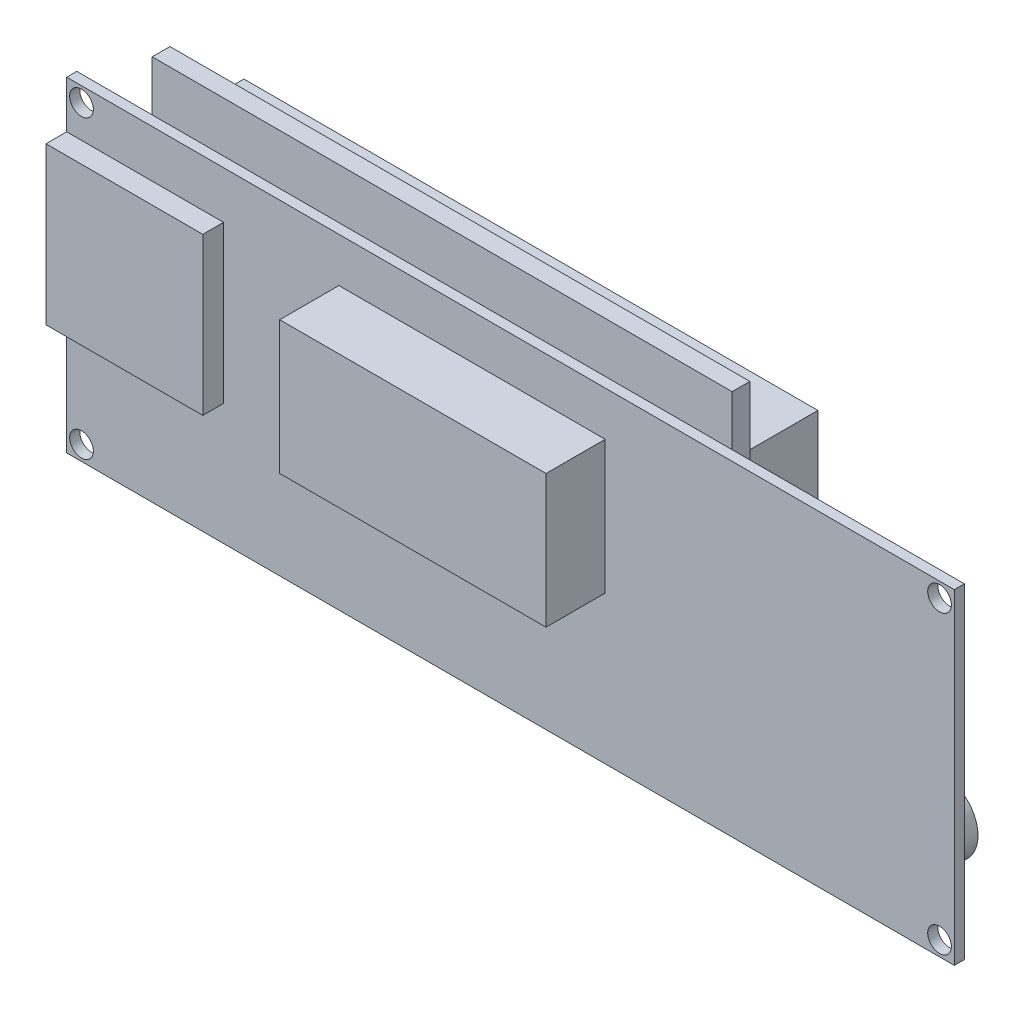
SolidWorks part; units mm, degrees
ref_plane "Front Plane" through (0, 0, 0) normal (0, 0, 1) x (1, 0, 0)
ref_plane "Top Plane" through (0, 0, 0) normal (0, 1, 0) x (1, 0, 0)
ref_plane "Right Plane" through (0, 0, 0) normal (1, 0, 0) x (0, 0, -1)
sketch "Sketch2" plane through (0, 0, 0) normal (0, 0, 1) x (1, 0, 0)
  line L0 (75, 27.5) -> (75, -27.5) construction
  line L1 (35.75, 27.5) -> (75, 27.5) construction
  line L2 (-75, -27.5) -> (75, -27.5) construction
  line L3 (-75, 27.5) -> (-75, -27.5) construction
  line L4 (-75, 27.5) -> (-62.25, 27.5) construction
  line L5 (-62.25, 27.5) -> (35.75, 27.5) construction
  line L6 (75, 27.5) -> (75, -27.5)
  line L7 (35.75, 27.5) -> (75, 27.5)
  line L8 (-75, -27.5) -> (75, -27.5)
  line L9 (-75, 27.5) -> (-75, -27.5)
  line L10 (-75, 27.5) -> (-62.25, 27.5)
  line L11 (-62.25, 27.5) -> (35.75, 27.5)
  circle A0 centre (-72.5, -25) radius 2 construction
  circle A1 centre (-72.5, 25) radius 2 construction
  circle A2 centre (72.5, -25) radius 2 construction
  circle A3 centre (72.5, 25) radius 2 construction
  circle A4 centre (-72.5, -25) radius 2
  circle A5 centre (-72.5, 25) radius 2
  circle A6 centre (72.5, -25) radius 2
  circle A7 centre (72.5, 25) radius 2
extrude "Boss-Extrude1" add sketch "Sketch2" along normal up to vertex (1.7 mm away)
sketch "Sketch3" plane through (0, 0, 0) normal (0, 0, 1) x (1, 0, 0)
  line L1 (-62.25, 36) -> (35.75, 36)
  line L2 (-62.25, 36) -> (-62.25, -24)
  line L3 (-62.25, -24) -> (35.75, -24)
  line L4 (35.75, 36) -> (35.75, -24)
  dimension "D1" = 60
extrude "Boss-Extrude2" add sketch "Sketch3" against normal up to vertex (3 mm away)
sketch "Sketch4" plane through (0, 0, 0) normal (0, 0, 1) x (1, 0, 0)
  line L1 (-61.75, -14.5) -> (35.25, -14.5)
  line L2 (-61.75, -14.5) -> (-61.75, 25.5)
  line L3 (-61.75, 25.5) -> (35.25, 25.5)
  line L4 (35.25, -14.5) -> (35.25, 25.5)
extrude "Boss-Extrude3" add sketch "Sketch4" against normal up to vertex (15 mm away)
sketch "Sketch5" plane through (0, 0, 0) normal (0, 0, 1) x (1, 0, 0)
  line L1 (59, 23) -> (65, 23)
  line L2 (59, 23) -> (59, 17)
  line L3 (59, 17) -> (65, 17)
  line L4 (65, 23) -> (65, 17)
  line L5 (59, 23) -> (65, 17) construction
  line L6 (59, 17) -> (65, 23) construction
  point P0 (62, 20)
  dimension "D1" = 6
  dimension "D2" = 6
extrude "Boss-Extrude4" add sketch "Sketch5" against normal blind 3
sketch "Sketch6" plane through (0, 0, -3) normal (0, 0, -1) x (-1, 0, 0)
  circle A0 centre (-62, 20) radius 1.75
  point P3 (-75, 27.5)
extrude "Boss-Extrude5" add sketch "Sketch6" along normal blind 0.65
sketch "Sketch7" plane through (0, 0, 0) normal (0, 0, 1) x (1, 0, 0)
  line L1 (55.875, -3.375) -> (68.125, -3.375)
  line L2 (55.875, -3.375) -> (55.875, 8.375)
  line L3 (55.875, 8.375) -> (68.125, 8.375)
  line L4 (68.125, -3.375) -> (68.125, 8.375)
  line L5 (55.875, -3.375) -> (68.125, 8.375) construction
  line L6 (55.875, 8.375) -> (68.125, -3.375) construction
  point P0 (62, 2.5)
  dimension "D1" = 11.75
  dimension "D2" = 12.25
extrude "Boss-Extrude6" add sketch "Sketch7" against normal blind 4.5
sketch "Sketch8" plane through (0, 0, 0) normal (0, 0, 1) x (1, 0, 0)
  circle A0 centre (62, -17.5) radius 6
  circle A1 centre (62, -17.5) radius 6 construction
extrude "Boss-Extrude7" add sketch "Sketch8" against normal blind 9.3
sketch "Sketch9" plane through (0, 0, 1.7) normal (0, 0, 1) x (1, 0, 0)
  line L0 (-75, -27.5) -> (75, -27.5) construction
  line L1 (16, -2.5) -> (-29, -2.5)
  line L2 (16, -2.5) -> (16, 20)
  line L3 (16, 20) -> (-29, 20)
  line L4 (-29, -2.5) -> (-29, 20)
  line L5 (-75, 27.5) -> (-75, -27.5) construction
  dimension "D1" = 45
  dimension "D2" = 22.5
  dimension "D3" = 25
  dimension "D4" = 46
extrude "Boss-Extrude8" add sketch "Sketch9" along normal up to vertex (10 mm away)
sketch "Sketch10" plane through (0, 0, 1.7) normal (0, 0, 1) x (1, 0, 0)
  line L0 (-75, 27.5) -> (-75, -27.5) construction
  line L1 (-75, 19.5) -> (-48.5, 19.5)
  line L2 (-75, 19.5) -> (-75, -7)
  line L3 (-75, -7) -> (-48.5, -7)
  line L4 (-48.5, 19.5) -> (-48.5, -7)
  line L5 (75, 27.5) -> (-75, 27.5) construction
  dimension "D1" = 26.5
  dimension "D2" = 26.5
  dimension "D3" = 8
extrude "Boss-Extrude9" add sketch "Sketch10" along normal blind 3.5
sketch "Sketch11" plane through (0, 0, -15) normal (0, 0, -1) x (-1, 0, 0)
  line L0 (13.25, -14.5) -> (13.25, 25.5) construction
  line L1 (61.75, -14.5) -> (-35.25, -14.5) construction
  line L2 (-35.25, 25.5) -> (61.75, 25.5) construction
  line L3 (61.75, 5.5) -> (-35.25, 5.5) construction
  line L4 (61.75, 25.5) -> (61.75, -14.5) construction
  line L5 (-35.25, -14.5) -> (-35.25, 25.5) construction
  line L7 (51.25, -7.5) -> (-24.75, -7.5)
  line L8 (51.25, -7.5) -> (51.25, 18.5)
  line L9 (51.25, 18.5) -> (-24.75, 18.5)
  line L10 (-24.75, -7.5) -> (-24.75, 18.5)
  line L11 (51.25, -7.5) -> (-24.75, 18.5) construction
  line L12 (51.25, 18.5) -> (-24.75, -7.5) construction
  point P12 (13.25, 5.5)
  point P13 (13.25, 5.5)
  dimension "D1" = 26
  dimension "D2" = 76
extrude "Cut-Extrude1" cut sketch "Sketch11" against normal blind 0.5
